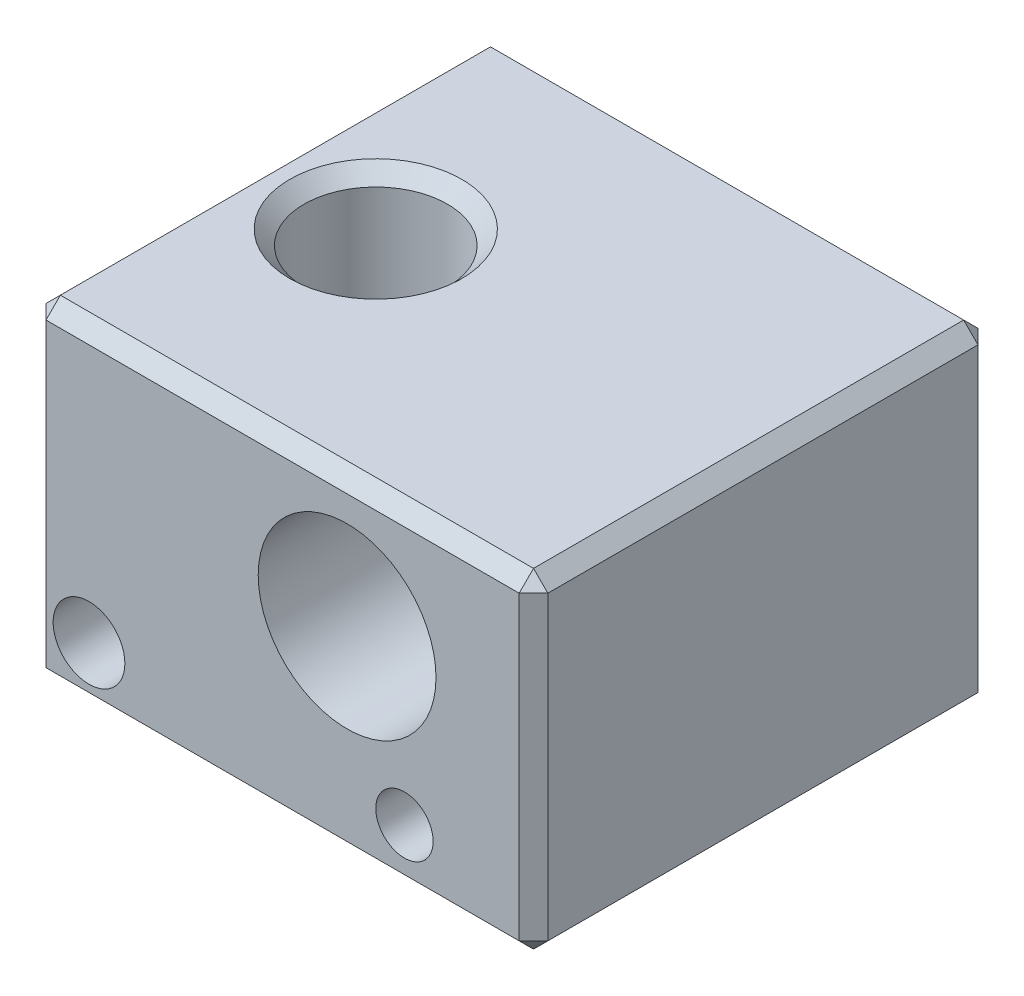
SolidWorks part; units mm, degrees
material "AISI 316 Annealed Stainless Steel Bar (SS)"
ref_plane "Front Plane" through (0, 0, 0) normal (0, 0, 1) x (1, 0, 0)
ref_plane "Top Plane" through (0, 0, 0) normal (0, 1, 0) x (1, 0, 0)
ref_plane "Right Plane" through (0, 0, 0) normal (1, 0, 0) x (0, 0, -1)
sketch "Sketch1" plane through (0, 0, 0) normal (0, 1, 0) x (1, 0, 0)
  line L1 (-8.75, -8) -> (8.75, -8)
  line L2 (-8.75, -8) -> (-8.75, 8)
  line L3 (-8.75, 8) -> (8.75, 8)
  line L4 (8.75, -8) -> (8.75, 8)
  line L5 (-8.75, -8) -> (8.75, 8) construction
  line L6 (-8.75, 8) -> (8.75, -8) construction
  point P0 (0, 0)
  dimension "D1" = 17.5
  dimension "D2" = 16
extrude "Boss-Extrude1" add sketch "Sketch1" along normal blind 11.5 contours L2 L3 L4 L1
sketch "Sketch2" plane through (0, 0, 8) normal (0, 0, 1) x (1, 0, 0)
  line L0 (-8.75, 11.5) -> (-8.75, 0) construction
  line L1 (-8.75, 0) -> (8.75, 0) construction
  circle A0 centre (2.25, 7) radius 3.1
  circle A1 centre (4.25, 2) radius 1
  dimension "D2" = 6.2
  dimension "D4" = 13
  dimension "D6" = 2
  dimension "D1" = 11
  dimension "D3" = 7
  dimension "D5" = 2
extrude "Cut-Extrude1" cut sketch "Sketch2" against normal through all
hole_wizard "Ø2.5 (2.5) Diameter Hole1" positions "Sketch4" profile "Sketch3" hole size "Ø2.5" standard "ANSI Metric"
sketch "Sketch4" plane through (0, 0, 8) normal (0, 0, 1) x (1, 0, 0)
  line L0 (-8.75, 11.5) -> (-8.75, 0) construction
  line L1 (-8.75, 0) -> (8.75, 0) construction
  point P0 (-6.75, 2)
  dimension "D1" = 2
  dimension "D2" = 2
sketch "Sketch3" plane through (-6.75, 2, 8) normal (1, 0, 0) x (0, -1, 0)
  line L0 (0, 0) -> (0, 4.5)
  line L1 (0, 4.5) -> (1.25, 4.5)
  line L2 (1.25, 4.5) -> (1.25, 0)
  line L5 (1.25, 0) -> (0, 0)
  line L10 (0, 4.5) -> (-1.25, 4.5) construction
  line L11 (0, -6.35) -> (0, 107.95) construction
  dimension "Hole Dia." = 2.5
  dimension "Hole Depth" = 4.5
  dimension "Drill Angle" = 180
hole_wizard "Tap Drill for M6x1.0 Tap1" positions "Sketch7" profile "Sketch6" hole size "M6x1.0" standard "ANSI Metric" end condition through all
sketch "Sketch7" plane through (0, 11.5, 0) normal (0, 1, 0) x (1, 0, 0)
  line L0 (-8.75, -8) -> (-8.75, 8) construction
  point P0 (-4.75, 0)
  dimension "D1" = 4
sketch "Sketch6" plane through (-4.75, 11.5, 0) normal (1, 0, 0) x (0, 0, 1)
  line L0 (0, 0) -> (0, 11.5)
  line L1 (0, 11.5) -> (2.5, 11.5)
  line L2 (2.5, 11.5) -> (2.5, 0)
  line L5 (2.5, 0) -> (0, 0)
  line L11 (0, -6.35) -> (0, 107.95) construction
  dimension "Thru Hole Dia." = 5
  dimension "Thru Hole Depth" = 11.5
hole_wizard "Tap Drill for M3x0.5 Tap1" positions "Sketch9" profile "Sketch8" hole size "M3x0.5" standard "ANSI Metric"
sketch "Sketch9" plane through (0, 0, 0) normal (0, -1, 0) x (-1, 0, 0)
  line L0 (8.75, -8) -> (8.75, 8) construction
  point P0 (-1.25, 0)
  dimension "D1" = 10
sketch "Sketch8" plane through (1.25, 0, 0) normal (1, 0, 0) x (0, 0, -1)
  line L0 (0, 0) -> (0, 7.7501)
  line L1 (0, 7.7501) -> (1.25, 6.999)
  line L2 (1.25, 6.999) -> (1.25, 0)
  line L5 (1.25, 0) -> (0, 0)
  line L10 (0, 7.7501) -> (-1.25, 6.999) construction
  line L11 (0, -6.35) -> (0, 107.95) construction
  dimension "Hole Dia." = 2.5
  dimension "Hole Depth" = 6.999
  dimension "Drill Angle" = 118
chamfer "Chamfer1" distance 0.5 angle 45 15 edges at (-4.75, 0, 2.5) (1.25, 0, -1.25) (-8.75, 5.75, -8) (-8.75, 5.75, 8) (8.75, 5.75, 8) (8.75, 0, 0) (0, 0, 8) (-8.75, 0, 0) (0, 0, -8) (8.75, 5.75, -8) (-8.75, 11.5, 0) (0, 11.5, -8) (8.75, 11.5, 0) (0, 11.5, 8) (-4.75, 11.5, 2.5)
